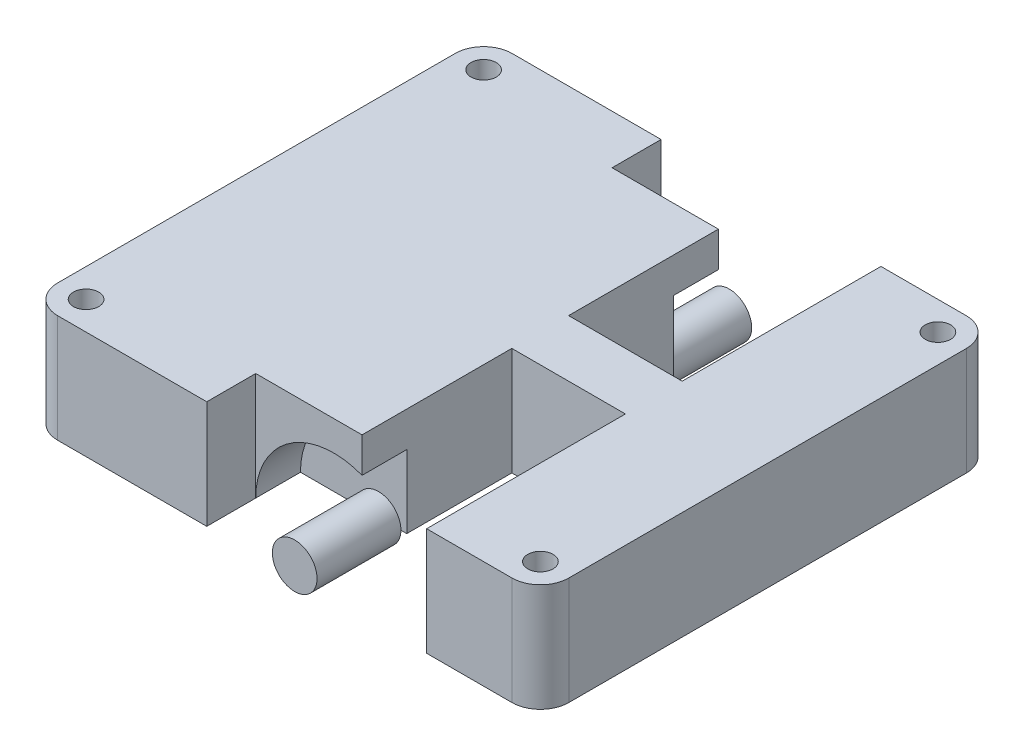
SolidWorks part; units mm, degrees
ref_plane "Front Plane" through (0, 0, 0) normal (0, 0, 1) x (1, 0, 0)
ref_plane "Top Plane" through (0, 0, 0) normal (0, 1, 0) x (1, 0, 0)
ref_plane "Right Plane" through (0, 0, 0) normal (1, 0, 0) x (0, 0, -1)
sketch "Sketch1" plane through (0, 0, 0) normal (0, 1, 0) x (1, 0, 0)
  line L1 (-22.86, 20.32) -> (22.86, 20.32)
  line L2 (-22.86, 20.32) -> (-22.86, -20.32)
  line L3 (-22.86, -20.32) -> (22.86, -20.32)
  line L4 (22.86, 20.32) -> (22.86, -20.32)
  line L5 (-22.86, 20.32) -> (22.86, -20.32) construction
  line L6 (-22.86, -20.32) -> (22.86, 20.32) construction
  point P0 (0, 0)
  dimension "D1" = 40.64
  dimension "D2" = 45.72
extrude "Body" add sketch "Sketch1" along normal mid plane 9.652
fillet "Corner Fillet" radius 2.54 4 edges at (22.86, 0, -20.32) (-22.86, 0, -20.32) (22.86, 0, 20.32) (-22.86, 0, 20.32)
hole_wizard "#4-40 Tapped Hole1" positions "Sketch2" profile "Sketch3" tap size "#4-40" standard "ANSI Inch" end condition through all
sketch "Sketch2" plane through (0, 4.826, 0) normal (0, 1, 0) x (1, 0, 0)
  line L1 (-20.32, -17.78) -> (20.32, -17.78)
  line L2 (-20.32, -17.78) -> (-20.32, 17.78)
  line L3 (-20.32, 17.78) -> (20.32, 17.78)
  line L4 (20.32, -17.78) -> (20.32, 17.78)
  line L5 (-20.32, -17.78) -> (20.32, 17.78) construction
  line L6 (-20.32, 17.78) -> (20.32, -17.78) construction
  point P2 (20.32, 17.78)
  point P63 (-20.32, -17.78)
  point P64 (-20.32, 17.78)
  point P65 (20.32, -17.78)
  dimension "D1" = 35.56
  dimension "D2" = 40.64
sketch "Sketch3" plane through (20.32, 4.826, -17.78) normal (1, 0, 0) x (0, 0, 1)
  line L0 (0, 0) -> (0, 9.652)
  line L1 (0, 9.652) -> (1.1303, 9.652)
  line L2 (1.1303, 9.652) -> (1.1303, 0)
  line L5 (1.1303, 0) -> (0, 0)
  line L11 (0, -6.35) -> (0, 107.95) construction
  dimension "Thru Tap Drill Dia." = 2.2606
  dimension "Thru Tap Drill Depth" = 9.652
cosmetic thread "Hole Thread1" parameters "D2"=2.8448
cosmetic thread "Hole Thread2" parameters "D2"=2.8448
cosmetic thread "Hole Thread3" parameters "D2"=2.8448
cosmetic thread "Hole Thread4" parameters "D2"=2.8448
sketch "Sketch4" plane through (0, 0, -20.32) normal (0, 0, -1) x (-1, 0, 0)
  line L0 (-20.32, -4.826) -> (20.32, -4.826) construction
  line L1 (-6.985, 4.826) -> (6.985, 4.826)
  line L2 (-6.985, 4.826) -> (-6.985, -4.826)
  line L3 (-6.985, -4.826) -> (6.985, -4.826)
  line L4 (6.985, 4.826) -> (6.985, -4.826)
  line L5 (-6.985, 4.826) -> (6.985, -4.826) construction
  line L6 (-6.985, -4.826) -> (6.985, 4.826) construction
  point P0 (0, 0)
  dimension "D1" = 13.97
extrude "Wheel Cutout" cut sketch "Sketch4" against normal blind 8.382
sketch "Sketch5" plane through (0, 0, -11.938) normal (0, 0, -1) x (-1, 0, 0)
  line L0 (-6.985, -4.826) -> (6.985, -4.826) construction
  circle A0 centre (0, -4.826) radius 2
  dimension "D1" = 4
extrude "Wheel Shaft" add sketch "Sketch5" along normal blind 7.5
sketch "Sketch9" plane through (0, 0, -20.32) normal (0, 0, -1) x (-1, 0, 0)
  line L0 (0, -4.826) -> (-7.6033, -4.826) construction
  line L1 (-7.6033, -4.826) -> (-7.6033, 0.174) construction
  line L2 (-7.6033, 0.174) -> (0, -4.826) construction
  line L3 (-12.6833, 4.826) -> (-12.6833, -4.826)
  line L4 (-20.32, 4.826) -> (-6.985, 4.826) construction
  line L5 (-20.32, -4.826) -> (-6.985, -4.826) construction
  line L6 (-12.6833, -4.826) -> (-2.5233, -4.826)
  line L7 (-2.5233, -4.826) -> (-2.5233, 4.826)
  line L8 (-2.5233, 4.826) -> (-12.6833, 4.826)
  circle A0 centre (-7.6033, 0.174) radius 4 construction
  circle A1 centre (-7.6033, 0.174) radius 5.08
  dimension "D3" = 8
  dimension "D4" = 10.16
  dimension "D1" = 9.1
  dimension "D2" = 5
extrude "Cut-Extrude2" cut sketch "Sketch9" against normal blind 17.78 contours L3 L6 L7 L8
sketch "Sketch10" plane through (0, 0, -11.938) normal (0, 0, -1) x (-1, 0, 0)
  line L1 (6.985, -4.826) -> (6.985, 4.826) construction
  line L2 (-2.5233, 4.826) -> (-2.5233, 1.6873)
  line L3 (-2.5233, -4.826) -> (-2.5233, 4.826) construction
  line L4 (6.985, 4.826) -> (-2.5233, 4.826) construction
  line L5 (6.985, -4.826) -> (6.985, 4.826)
  line L6 (6.985, 4.826) -> (-2.5233, 4.826)
  circle A0 centre (0, -4.826) radius 6.985
  line M2 (-2.5233, 4.826) -> (-2.5233, -4.826)
  line M6 (6.985, -4.826) -> (6.985, 4.826)
  line M7 (6.985, 4.826) -> (-2.5233, 4.826)
extrude "Boss-Extrude2" add sketch "Sketch10" along normal blind 4 contours A0 M6 M7 M2
mirror "Mirror3" about plane through (0, 0, 0) normal (0, 0, 1) of "Cut-Extrude2", "Wheel Cutout", "Wheel Shaft", "Boss-Extrude2"
